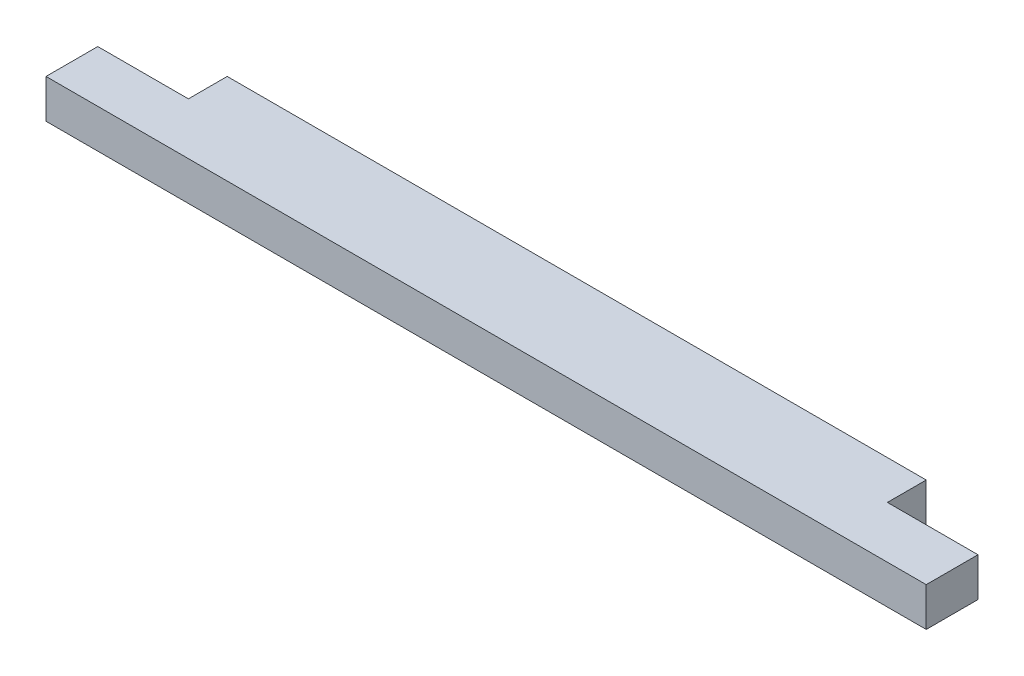
SolidWorks part; units mm, degrees
material "Pine"
ref_plane "Front Plane" through (0, 0, 0) normal (0, 0, 1) x (1, 0, 0)
ref_plane "Top Plane" through (0, 0, 0) normal (0, 1, 0) x (1, 0, 0)
ref_plane "Right Plane" through (0, 0, 0) normal (1, 0, 0) x (0, 0, -1)
sketch "Sketch1" plane through (0, 0, 0) normal (0, 1, 0) x (1, 0, 0)
  line L1 (0, 0) -> (863.6, 0)
  line L2 (0, 0) -> (0, 88.9)
  line L3 (0, 88.9) -> (863.6, 88.9)
  line L4 (863.6, 0) -> (863.6, 88.9)
  dimension "D1" = 88.9
  dimension "D2" = 863.6
extrude "Boss-Extrude1" add sketch "Sketch1" along normal blind 38.1
sketch "Sketch3" plane through (0, 38.1, 0) normal (0, 1, 0) x (1, 0, 0)
  line L5 (863.6, 88.9) -> (774.7, 88.9)
  line L6 (863.6, 88.9) -> (863.6, 50.8)
  line L7 (863.6, 50.8) -> (774.7, 50.8)
  line L8 (774.7, 88.9) -> (774.7, 50.8)
  line L9 (0, 88.9) -> (88.9, 88.9)
  line L10 (0, 88.9) -> (0, 50.8)
  line L11 (0, 50.8) -> (88.9, 50.8)
  line L12 (88.9, 88.9) -> (88.9, 50.8)
  dimension "D2" = 88.9
  dimension "D4" = 38.1
extrude "Cut-Extrude1" cut sketch "Sketch3" against normal through all
